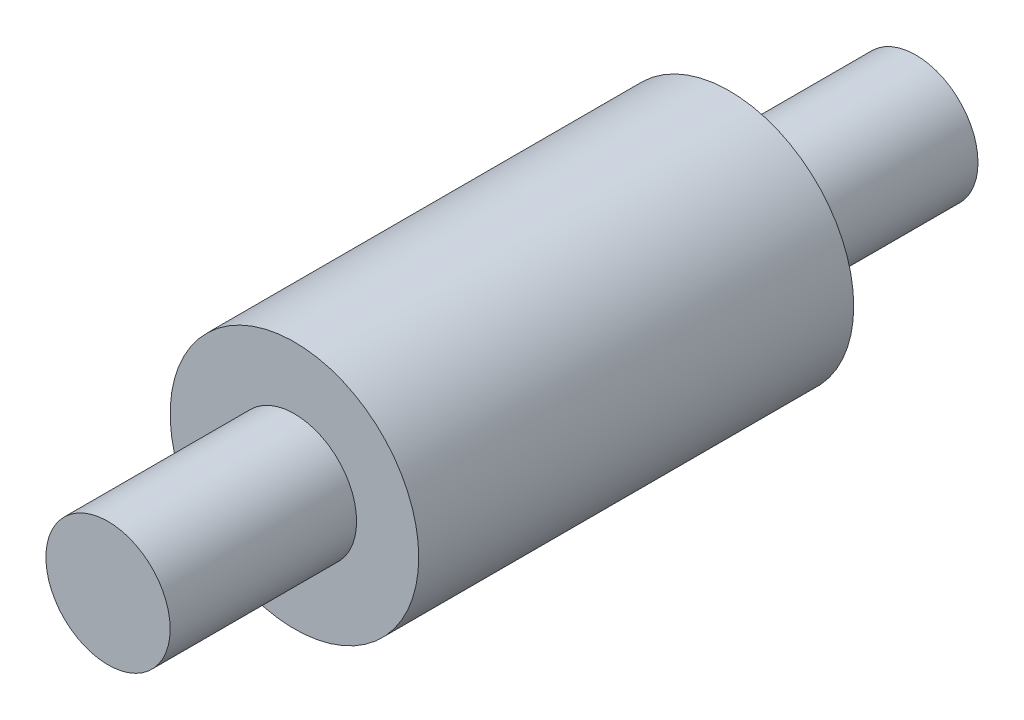
SolidWorks part; units mm, degrees
material "AISI 4130 Steel, normalized at 870C"
ref_plane "Front Plane" through (0, 0, 0) normal (0, 0, 1) x (1, 0, 0)
ref_plane "Top Plane" through (0, 0, 0) normal (0, 1, 0) x (1, 0, 0)
ref_plane "Right Plane" through (0, 0, 0) normal (1, 0, 0) x (0, 0, -1)
sketch "Sketch1" plane through (0, 0, 0) normal (1, 0, 0) x (0, 0, -1)
  line L0 (-43.2424, 0) -> (122.8633, 0) construction
  line L1 (0, 0) -> (0, 10)
  line L2 (0, 10) -> (30, 10)
  line L3 (30, 10) -> (30, 20)
  line L4 (30, 20) -> (100, 20)
  line L5 (100, 20) -> (100, 10)
  line L6 (100, 10) -> (130, 10)
  line L7 (130, 10) -> (130, 0)
  line L8 (130, 0) -> (0, 0)
revolve "Revolve1" add sketch "Sketch1" angle 360 about L0
